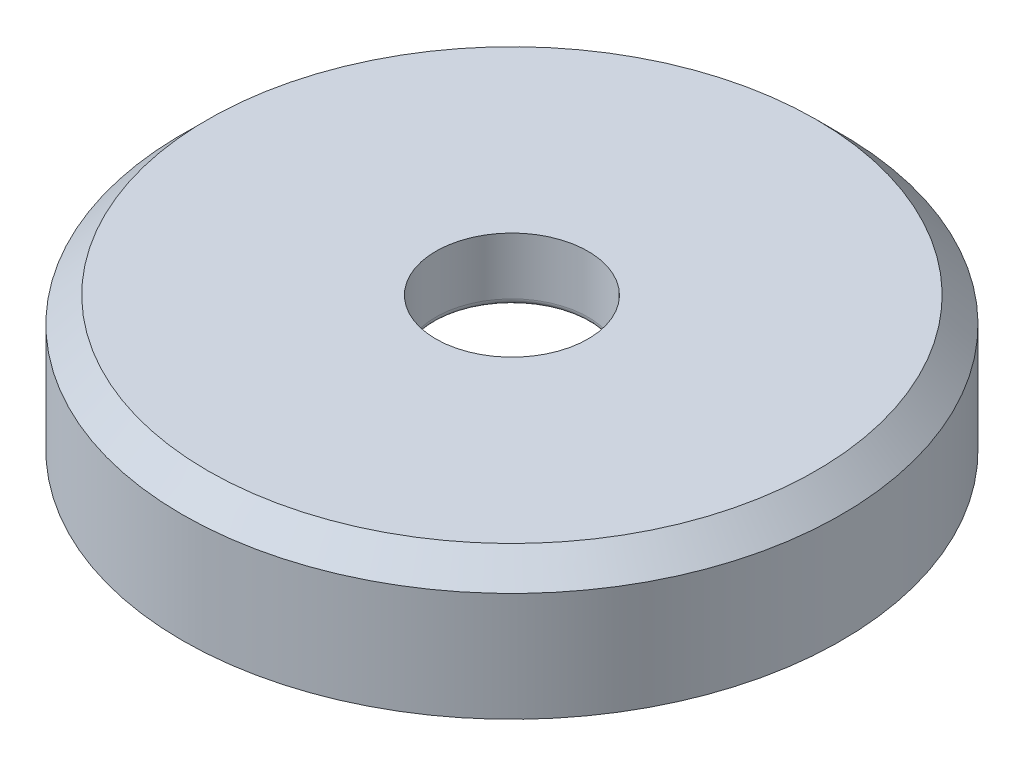
SolidWorks part; units mm, degrees
ref_plane "Front Plane" through (0, 0, 0) normal (0, 0, 1) x (1, 0, 0)
ref_plane "Top Plane" through (0, 0, 0) normal (0, 1, 0) x (1, 0, 0)
ref_plane "Right Plane" through (0, 0, 0) normal (1, 0, 0) x (0, 0, -1)
sketch "Sketch1" plane through (0, 0, 0) normal (0, 1, 0) x (1, 0, 0)
  line L1 (0, -9.9593) -> (8.625, -4.9796)
  line L2 (8.625, -4.9796) -> (8.625, 4.9796)
  line L3 (8.625, 4.9796) -> (0, 9.9593)
  line L4 (0, 9.9593) -> (-8.625, 4.9796)
  line L5 (-8.625, 4.9796) -> (-8.625, -4.9796)
  line L6 (-8.625, -4.9796) -> (0, -9.9593)
  circle A0 centre (0, 0) radius 8.625 construction
  circle A1 centre (0, 0) radius 13
  dimension "D2" = 26
  dimension "D1" = 17.25
extrude "Boss-Extrude1" add sketch "Sketch1" along normal blind 2.8
sketch "Sketch2" plane through (0, 2.8, 0) normal (0, 1, 0) x (1, 0, 0)
  circle A0 centre (0, 0) radius 13 construction
  circle A1 centre (0, 0) radius 13
  circle A2 centre (0, 0) radius 3
  dimension "D1" = 6
extrude "Boss-Extrude2" add sketch "Sketch2" along normal blind 2.5
chamfer "Chamfer1" distance 1 angle 45 1 edges at (0, 5.3, 13)
fillet "Fillet1" radius 0.25 1 edges at (0, 2.8, 3)
